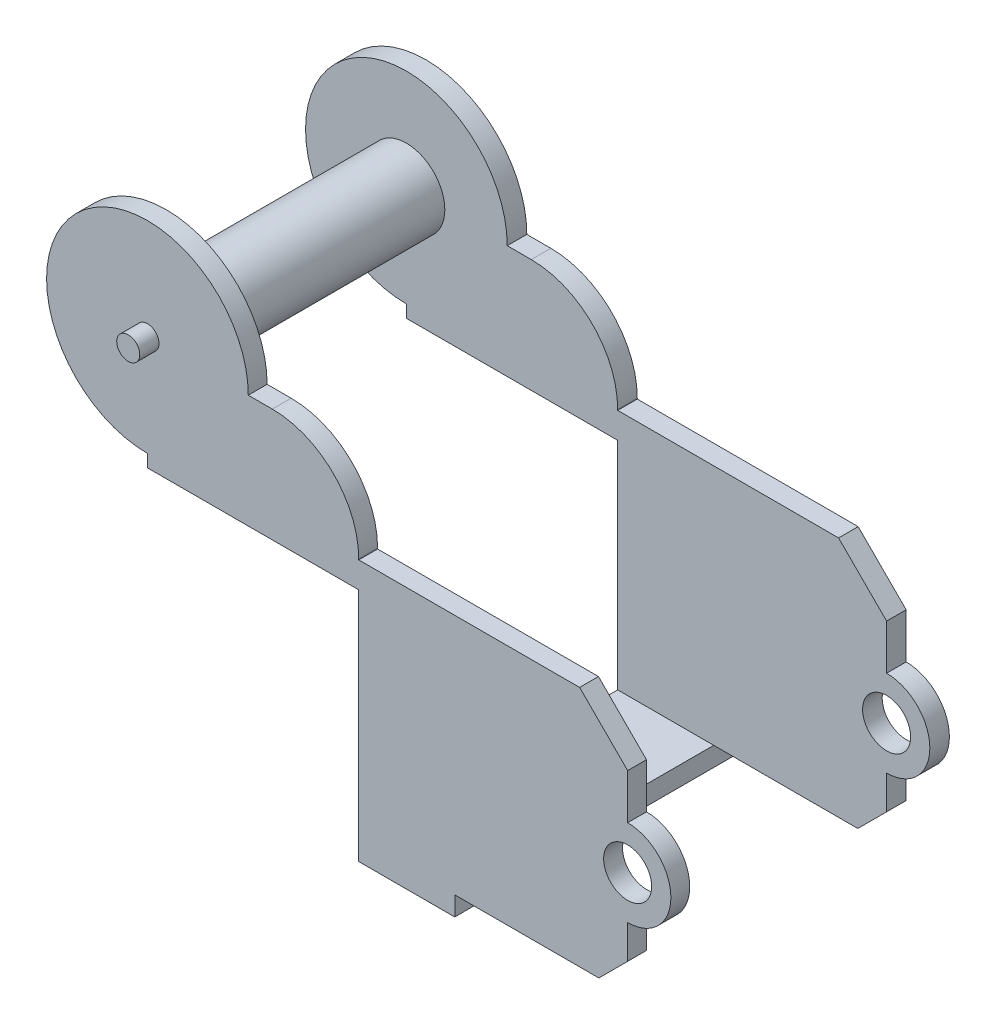
SolidWorks part; units mm, degrees
ref_plane "前视基准面" through (0, 0, 0) normal (0, 0, 1) x (1, 0, 0)
ref_plane "上视基准面" through (0, 0, 0) normal (0, 1, 0) x (1, 0, 0)
ref_plane "右视基准面" through (0, 0, 0) normal (1, 0, 0) x (0, 0, -1)
sketch "草图1" plane through (0, 0, 0) normal (0, 0, 1) x (1, 0, 0)
  line L6 (4.4375, 17.7993) -> (4.4375, 22.5002)
  line L7 (-0.5625, 27.5002) -> (-23.5625, 27.5002)
  line L10 (4.4375, 8.7985) -> (4.4375, 5.2979)
  line L13 (-0.5625, 27.5002) -> (-23.5625, 27.5002)
  line L14 (4.4375, 22.5002) -> (4.4375, 17.7993)
  line L15 (1.4375, 2.2979) -> (-13.5625, 2.2979)
  line L16 (-23.5625, 24.7989) -> (-23.5625, 2.2979)
  line L17 (4.4375, 8.7985) -> (4.4375, 5.2979)
  line L18 (-23.5625, 27.5002) -> (-23.5625, 27.5989)
  line L19 (-23.5625, 13.2989) -> (-23.5625, 24.7989)
  line L20 (-32.5625, 36.5989) -> (-35.0625, 36.5989)
  line L21 (-23.5625, 24.7989) -> (-45.5625, 24.7989)
  line L22 (-45.5625, 24.7989) -> (-45.5625, 26.0989)
  line L23 (-23.5625, 2.2979) -> (-23.5625, 0.2979)
  line L24 (-23.5625, 0.2979) -> (-13.5625, 0.2979)
  line L25 (-13.5625, 0.2979) -> (-13.5625, 2.2979)
  line L26 (4.4375, 22.5002) -> (-0.5625, 27.5002)
  line L27 (4.4375, 5.2979) -> (1.4375, 2.2979)
  circle A0 centre (4.4375, 13.2989) radius 2.5002
  arc A1 (4.4375, 8.7985) -> (4.4375, 17.7993) centre (4.4375, 13.2989) ccw
  arc A3 (-35.0625, 36.5989) -> (-45.5625, 26.0989) centre (-45.5625, 36.5989) ccw
  arc A4 (-23.5625, 27.5989) -> (-32.5625, 36.5989) centre (-32.5625, 27.5989) ccw
  circle A5 centre (-45.5625, 36.5989) radius 4
  point P6 (0, 0)
  dimension "D1" = 11.5
  dimension "D2" = 9
extrude "凸台-拉伸3" add sketch "草图1" along normal blind 29 contours L18 A4 L20 A3 L22 L21 L16 L23 L24 L25 L15 L27 L10 A1 L6 L26 L7 A5 A0
sketch "草图5" plane through (0, 2.2979, 0) normal (0, -1, 0) x (1, 0, 0)
  line L0 (-13.5625, 27.038) -> (-13.5625, 2.038)
  line L3 (-13.5625, 27.038) -> (16.2508, 27.038)
  line L5 (-13.5625, 2.038) -> (16.2508, 2.038)
  line L6 (16.2508, 27.038) -> (16.2508, 2.038)
  point P5 (-13.5625, 14.538)
extrude "切除-拉伸2" cut sketch "草图5" against normal blind 50
sketch "草图6" plane through (-13.5625, 0, 0) normal (1, 0, 0) x (0, 0, -1)
  line L1 (-2.038, 2.2979) -> (-27.038, 2.2979)
  line L2 (-2.038, 2.2979) -> (-2.038, 56.3535)
  line L3 (-2.038, 56.3535) -> (-27.038, 56.3535)
  line L4 (-27.038, 2.2979) -> (-27.038, 56.3535)
extrude "切除-拉伸3" cut sketch "草图6" against normal blind 50
sketch "草图7" plane through (0, 0, 29) normal (0, 0, 1) x (1, 0, 0)
  circle A0 centre (-45.5625, 36.5989) radius 4
  circle A1 centre (-45.5625, 36.5989) radius 1.2
extrude "凸台-拉伸4" add sketch "草图7" against normal blind 29
sketch "草图10" plane through (0, 0, 0) normal (0, 0, -1) x (-1, 0, 0)
  circle A0 centre (45.5625, 36.5989) radius 1.2
extrude "凸台-拉伸5" add sketch "草图10" along normal blind 2 and the other way blind 31
